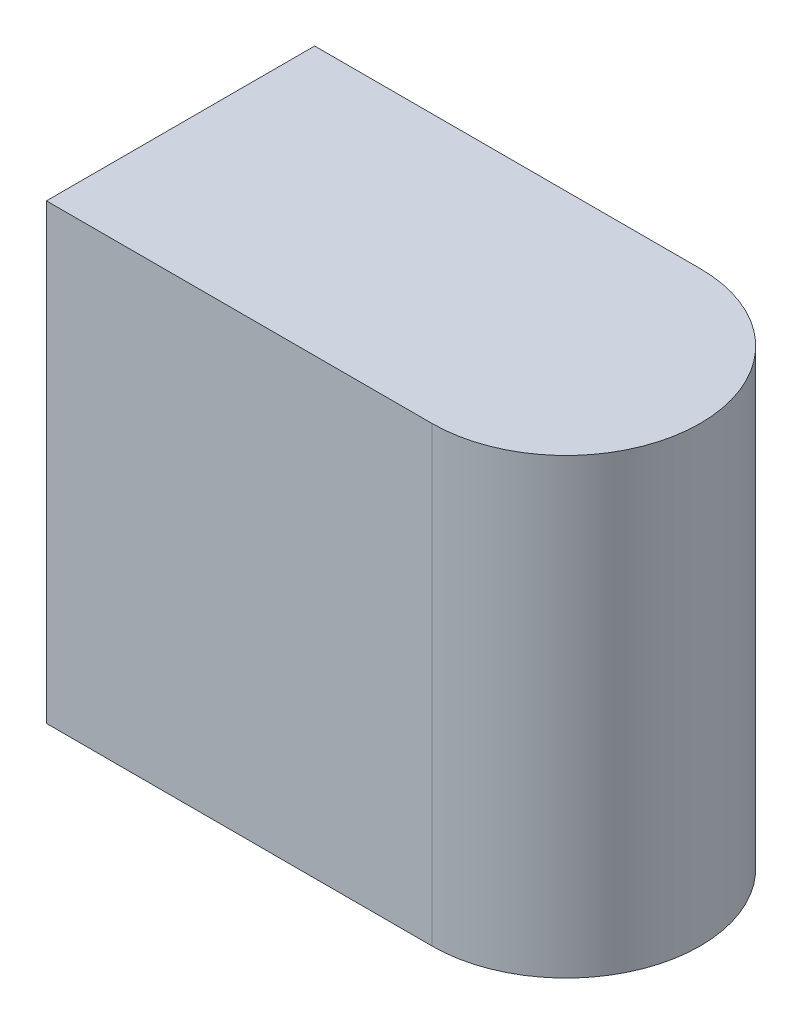
SolidWorks part; units mm, degrees
ref_plane "Přední rovina" through (0, 0, 0) normal (0, 0, 1) x (1, 0, 0)
ref_plane "Vrchní rovina" through (0, 0, 0) normal (0, 1, 0) x (1, 0, 0)
ref_plane "Pravá rovina" through (0, 0, 0) normal (1, 0, 0) x (0, 0, -1)
sketch "Skica1" plane through (0, 0, 0) normal (0, 1, 0) x (1, 0, 0)
  line L0 (0, 0) -> (0, 8)
  line L1 (0, 8) -> (11.5, 8)
  line L2 (11.5, 0) -> (0, 0)
  arc A0 (11.5, 8) -> (11.5, 0) centre (11.5, 4) cw
  point P6 (14.1791, 0)
  dimension "D1" = 8
  dimension "D2" = 15.5
extrude "Přidat vysunutím1" add sketch "Skica1" along normal blind 13.5
